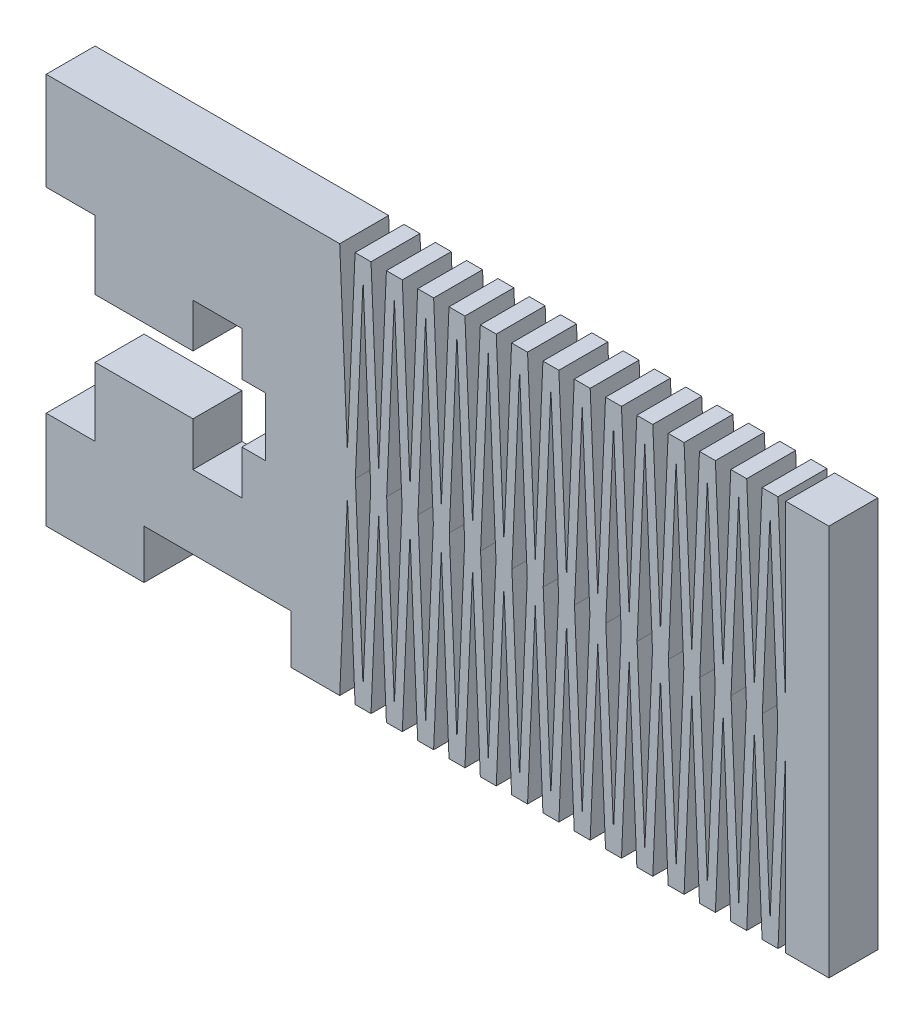
SolidWorks part; units mm, degrees
ref_plane "Front Plane" through (0, 0, 0) normal (0, 0, 1) x (1, 0, 0)
ref_plane "Top Plane" through (0, 0, 0) normal (0, 1, 0) x (1, 0, 0)
ref_plane "Right Plane" through (0, 0, 0) normal (1, 0, 0) x (0, 0, -1)
sketch "Sketch1" plane through (0, 0, 0) normal (0, 0, 1) x (1, 0, 0)
  line L0 (0, 12.7) -> (50.8, 12.7) construction
  line L1 (0, 0) -> (6.35, 0)
  line L2 (0, 0) -> (0, 25.4)
  line L3 (0, 25.4) -> (50.8, 25.4)
  line L4 (50.8, 0) -> (50.8, 25.4)
  line L5 (0, 19.05) -> (3.175, 19.05)
  line L6 (3.175, 19.05) -> (3.175, 14.605)
  line L7 (3.175, 14.605) -> (9.525, 14.605)
  line L8 (9.525, 14.605) -> (9.525, 17.4625)
  line L9 (9.525, 17.4625) -> (12.7, 17.4625)
  line L10 (12.7, 17.4625) -> (12.7, 14.605)
  line L11 (12.7, 14.605) -> (14.224, 14.605)
  line L12 (14.224, 14.605) -> (14.224, 10.795)
  line L13 (12.7, 10.795) -> (14.224, 10.795)
  line L14 (12.7, 7.9375) -> (12.7, 10.795)
  line L15 (9.525, 7.9375) -> (12.7, 7.9375)
  line L16 (19.05, 25.4) -> (19.05, 0) construction
  line L17 (19.05, 13.97) -> (50.8, 13.97) construction
  line L18 (19.05, 11.43) -> (50.8, 11.43) construction
  line L19 (19.05, 25.4) -> (19.549, 13.97)
  line L20 (19.549, 13.97) -> (20.0481, 25.4)
  line L21 (19.549, 13.97) -> (19.549, 25.4) construction
  line L22 (19.05, 24.13) -> (50.8, 24.13) construction
  line L23 (20.565, 24.13) -> (20.066, 12.7)
  line L24 (20.565, 24.13) -> (20.565, 25.4) construction
  line L25 (21.082, 25.4) -> (21.581, 13.97)
  line L26 (20.565, 24.13) -> (21.0641, 12.7)
  line L27 (20.565, 24.13) -> (20.565, 12.7) construction
  line L28 (21.082, 0) -> (21.581, 11.43)
  line L29 (20.565, 1.27) -> (21.0641, 12.7)
  line L30 (20.565, 1.27) -> (20.066, 12.7)
  line L31 (19.549, 11.43) -> (20.0481, 0)
  line L32 (19.05, 0) -> (19.549, 11.43)
  line L33 (21.581, 13.97) -> (22.0801, 25.4)
  line L34 (22.597, 24.13) -> (22.098, 12.7)
  line L35 (22.597, 24.13) -> (23.0961, 12.7)
  line L36 (23.114, 25.4) -> (23.613, 13.97)
  line L37 (21.581, 11.43) -> (22.0801, 0)
  line L38 (22.597, 1.27) -> (22.098, 12.7)
  line L39 (22.597, 1.27) -> (23.0961, 12.7)
  line L40 (23.114, 0) -> (23.613, 11.43)
  line L41 (23.613, 13.97) -> (24.1121, 25.4)
  line L42 (24.629, 24.13) -> (24.13, 12.7)
  line L43 (24.629, 24.13) -> (25.1281, 12.7)
  line L44 (25.146, 25.4) -> (25.645, 13.97)
  line L45 (23.613, 11.43) -> (24.1121, 0)
  line L46 (24.629, 1.27) -> (24.13, 12.7)
  line L47 (24.629, 1.27) -> (25.1281, 12.7)
  line L48 (25.146, 0) -> (25.645, 11.43)
  line L49 (25.645, 13.97) -> (26.1441, 25.4)
  line L50 (26.661, 24.13) -> (26.162, 12.7)
  line L51 (26.661, 24.13) -> (27.1601, 12.7)
  line L52 (27.178, 25.4) -> (27.677, 13.97)
  line L53 (25.645, 11.43) -> (26.1441, 0)
  line L54 (26.661, 1.27) -> (26.162, 12.7)
  line L55 (26.661, 1.27) -> (27.1601, 12.7)
  line L56 (27.178, 0) -> (27.677, 11.43)
  line L57 (27.677, 13.97) -> (28.1761, 25.4)
  line L58 (28.693, 24.13) -> (28.194, 12.7)
  line L59 (28.693, 24.13) -> (29.1921, 12.7)
  line L60 (29.21, 25.4) -> (29.709, 13.97)
  line L61 (27.677, 11.43) -> (28.1761, 0)
  line L62 (28.693, 1.27) -> (28.194, 12.7)
  line L63 (28.693, 1.27) -> (29.1921, 12.7)
  line L64 (29.21, 0) -> (29.709, 11.43)
  line L65 (29.709, 13.97) -> (30.2081, 25.4)
  line L66 (30.725, 24.13) -> (30.226, 12.7)
  line L67 (30.725, 24.13) -> (31.2241, 12.7)
  line L68 (31.242, 25.4) -> (31.741, 13.97)
  line L69 (29.709, 11.43) -> (30.2081, 0)
  line L70 (30.725, 1.27) -> (30.226, 12.7)
  line L71 (30.725, 1.27) -> (31.2241, 12.7)
  line L72 (31.242, 0) -> (31.741, 11.43)
  line L73 (31.741, 13.97) -> (32.2401, 25.4)
  line L74 (32.757, 24.13) -> (32.258, 12.7)
  line L75 (32.757, 24.13) -> (33.2561, 12.7)
  line L76 (33.274, 25.4) -> (33.773, 13.97)
  line L77 (31.741, 11.43) -> (32.2401, 0)
  line L78 (32.757, 1.27) -> (32.258, 12.7)
  line L79 (32.757, 1.27) -> (33.2561, 12.7)
  line L80 (33.274, 0) -> (33.773, 11.43)
  line L81 (33.773, 13.97) -> (34.2721, 25.4)
  line L82 (34.789, 24.13) -> (34.29, 12.7)
  line L83 (34.789, 24.13) -> (35.2881, 12.7)
  line L84 (35.306, 25.4) -> (35.805, 13.97)
  line L85 (33.773, 11.43) -> (34.2721, 0)
  line L86 (34.789, 1.27) -> (34.29, 12.7)
  line L87 (34.789, 1.27) -> (35.2881, 12.7)
  line L88 (35.306, 0) -> (35.805, 11.43)
  line L89 (35.805, 13.97) -> (36.3041, 25.4)
  line L90 (36.821, 24.13) -> (36.322, 12.7)
  line L91 (36.821, 24.13) -> (37.3201, 12.7)
  line L92 (37.338, 25.4) -> (37.837, 13.97)
  line L93 (35.805, 11.43) -> (36.3041, 0)
  line L94 (36.821, 1.27) -> (36.322, 12.7)
  line L95 (36.821, 1.27) -> (37.3201, 12.7)
  line L96 (37.338, 0) -> (37.837, 11.43)
  line L97 (37.837, 13.97) -> (38.3361, 25.4)
  line L98 (38.853, 24.13) -> (38.354, 12.7)
  line L99 (38.853, 24.13) -> (39.3521, 12.7)
  line L100 (39.37, 25.4) -> (39.869, 13.97)
  line L101 (37.837, 11.43) -> (38.3361, 0)
  line L102 (38.853, 1.27) -> (38.354, 12.7)
  line L103 (38.853, 1.27) -> (39.3521, 12.7)
  line L104 (39.37, 0) -> (39.869, 11.43)
  line L105 (39.869, 13.97) -> (40.3681, 25.4)
  line L106 (40.885, 24.13) -> (40.386, 12.7)
  line L107 (40.885, 24.13) -> (41.3841, 12.7)
  line L108 (41.402, 25.4) -> (41.901, 13.97)
  line L109 (39.869, 11.43) -> (40.3681, 0)
  line L110 (40.885, 1.27) -> (40.386, 12.7)
  line L111 (40.885, 1.27) -> (41.3841, 12.7)
  line L112 (41.402, 0) -> (41.901, 11.43)
  line L113 (41.901, 13.97) -> (42.4001, 25.4)
  line L114 (42.917, 24.13) -> (42.418, 12.7)
  line L115 (42.917, 24.13) -> (43.4161, 12.7)
  line L116 (43.434, 25.4) -> (43.933, 13.97)
  line L117 (41.901, 11.43) -> (42.4001, 0)
  line L118 (42.917, 1.27) -> (42.418, 12.7)
  line L119 (42.917, 1.27) -> (43.4161, 12.7)
  line L120 (43.434, 0) -> (43.933, 11.43)
  line L121 (43.933, 13.97) -> (44.4321, 25.4)
  line L122 (44.949, 24.13) -> (44.45, 12.7)
  line L123 (44.949, 24.13) -> (45.4481, 12.7)
  line L124 (45.466, 25.4) -> (45.965, 13.97)
  line L125 (43.933, 11.43) -> (44.4321, 0)
  line L126 (44.949, 1.27) -> (44.45, 12.7)
  line L127 (44.949, 1.27) -> (45.4481, 12.7)
  line L128 (45.466, 0) -> (45.965, 11.43)
  line L129 (45.965, 13.97) -> (46.4641, 25.4)
  line L130 (46.981, 24.13) -> (46.482, 12.7)
  line L131 (46.981, 24.13) -> (47.4801, 12.7)
  line L132 (47.498, 25.4) -> (47.997, 13.97)
  line L133 (45.965, 11.43) -> (46.4641, 0)
  line L134 (46.981, 1.27) -> (46.482, 12.7)
  line L135 (46.981, 1.27) -> (47.4801, 12.7)
  line L136 (47.498, 0) -> (47.997, 11.43)
  line L137 (47.997, 13.97) -> (47.997, 25.4)
  line L138 (47.997, 11.43) -> (47.997, 0)
  line L139 (6.35, 0) -> (6.35, 3.175)
  line L140 (6.35, 3.175) -> (15.875, 3.175)
  line L141 (15.875, 3.175) -> (15.875, 0)
  line L142 (15.875, 0) -> (50.8, 0)
  line L227 (9.525, 10.795) -> (9.525, 7.9375)
  line L228 (3.175, 10.795) -> (9.525, 10.795)
  line L229 (3.175, 6.35) -> (3.175, 10.795)
  line L230 (0, 6.35) -> (3.175, 6.35)
  line L231 (63.237, 24.13) -> (62.738, 12.7) [skipped]
  line L232 (64.253, 13.97) -> (64.7521, 25.4) [skipped]
  line L233 (65.269, 24.13) -> (64.77, 12.7) [skipped]
  line L234 (63.237, 24.13) -> (63.7361, 12.7) [skipped]
  line L235 (67.818, 25.4) -> (68.317, 13.97) [skipped]
  line L236 (69.333, 24.13) -> (68.834, 12.7) [skipped]
  line L237 (69.85, 25.4) -> (70.349, 13.97) [skipped]
  line L238 (69.333, 24.13) -> (69.8321, 12.7) [skipped]
  line L239 (68.317, 13.97) -> (68.8161, 25.4) [skipped]
  line L240 (65.269, 24.13) -> (65.7681, 12.7) [skipped]
  line L241 (63.754, 25.4) -> (64.253, 13.97) [skipped]
  line L242 (68.317, 11.43) -> (68.8161, 0) [skipped]
  line L243 (69.85, 0) -> (70.349, 11.43) [skipped]
  line L244 (67.818, 0) -> (68.317, 11.43) [skipped]
  line L245 (65.269, 1.27) -> (65.7681, 12.7) [skipped]
  line L246 (63.754, 0) -> (64.253, 11.43) [skipped]
  line L247 (61.722, 0) -> (62.221, 11.43) [skipped]
  line L248 (63.237, 1.27) -> (62.738, 12.7) [skipped]
  line L249 (62.221, 11.43) -> (62.7201, 0) [skipped]
  line L250 (65.269, 1.27) -> (64.77, 12.7) [skipped]
  line L251 (65.786, 0) -> (66.285, 11.43) [skipped]
  line L252 (66.285, 11.43) -> (66.7841, 0) [skipped]
  line L253 (67.301, 1.27) -> (66.802, 12.7) [skipped]
  line L254 (67.301, 1.27) -> (67.8001, 12.7) [skipped]
  line L255 (69.333, 1.27) -> (68.834, 12.7) [skipped]
  line L256 (69.333, 1.27) -> (69.8321, 12.7) [skipped]
  line L257 (67.301, 24.13) -> (66.802, 12.7) [skipped]
  line L258 (67.301, 24.13) -> (67.8001, 12.7) [skipped]
  line L259 (66.285, 13.97) -> (66.7841, 25.4) [skipped]
  line L260 (65.786, 25.4) -> (66.285, 13.97) [skipped]
  line L261 (64.253, 11.43) -> (64.7521, 0) [skipped]
  line L262 (63.237, 1.27) -> (63.7361, 12.7) [skipped]
  line L263 (59.173, 1.27) -> (59.6721, 12.7) [skipped]
  line L264 (60.189, 11.43) -> (60.6881, 0) [skipped]
  line L265 (61.205, 1.27) -> (60.706, 12.7) [skipped]
  line L266 (61.205, 1.27) -> (61.7041, 12.7) [skipped]
  line L267 (59.69, 25.4) -> (60.189, 13.97) [skipped]
  line L268 (59.173, 24.13) -> (59.6721, 12.7) [skipped]
  line L269 (61.205, 24.13) -> (61.7041, 12.7) [skipped]
  line L270 (59.173, 24.13) -> (58.674, 12.7) [skipped]
  line L271 (58.157, 13.97) -> (58.6561, 25.4) [skipped]
  line L272 (57.658, 25.4) -> (58.157, 13.97) [skipped]
  line L273 (57.141, 24.13) -> (56.642, 12.7) [skipped]
  line L274 (55.109, 24.13) -> (55.6081, 12.7) [skipped]
  line L275 (54.093, 13.97) -> (54.5921, 25.4) [skipped]
  line L276 (57.141, 1.27) -> (56.642, 12.7) [skipped]
  line L277 (59.69, 0) -> (60.189, 11.43) [skipped]
  line L278 (60.189, 13.97) -> (60.6881, 25.4) [skipped]
  line L279 (61.722, 25.4) -> (62.221, 13.97) [skipped]
  line L280 (56.125, 13.97) -> (56.6241, 25.4) [skipped]
  line L281 (56.125, 11.43) -> (56.6241, 0) [skipped]
  line L282 (57.141, 1.27) -> (57.6401, 12.7) [skipped]
  line L283 (57.141, 24.13) -> (57.6401, 12.7) [skipped]
  line L284 (52.061, 13.97) -> (52.5601, 25.4) [skipped]
  line L285 (53.077, 24.13) -> (52.578, 12.7) [skipped]
  line L286 (51.562, 25.4) -> (52.061, 13.97) [skipped]
  line L287 (51.045, 24.13) -> (51.5441, 12.7) [skipped]
  line L288 (51.045, 1.27) -> (51.5441, 12.7) [skipped]
  line L289 (51.562, 0) -> (52.061, 11.43) [skipped]
  line L290 (52.061, 11.43) -> (52.5601, 0) [skipped]
  line L291 (53.077, 1.27) -> (52.578, 12.7) [skipped]
  line L292 (53.594, 0) -> (54.093, 11.43) [skipped]
  line L293 (53.077, 1.27) -> (53.5761, 12.7) [skipped]
  line L294 (53.077, 24.13) -> (53.5761, 12.7) [skipped]
  line L295 (51.045, 24.13) -> (50.546, 12.7) [skipped]
  line L296 (51.045, 1.27) -> (50.546, 12.7) [skipped]
  line L297 (50.029, 11.43) -> (50.5281, 0) [skipped]
  line L298 (49.53, 25.4) -> (50.029, 13.97) [skipped]
  line L299 (49.53, 0) -> (50.029, 11.43) [skipped]
  line L300 (50.029, 13.97) -> (50.5281, 25.4) [skipped]
  line L301 (49.013, 24.13) -> (49.5121, 12.7) [skipped]
  line L302 (49.013, 1.27) -> (49.5121, 12.7) [skipped]
  line L303 (49.013, 24.13) -> (48.514, 12.7) [skipped]
  line L304 (49.013, 1.27) -> (48.514, 12.7) [skipped]
  line L305 (47.997, 13.97) -> (48.4961, 25.4) [skipped]
  line L306 (47.997, 11.43) -> (48.4961, 0) [skipped]
  line L307 (53.594, 25.4) -> (54.093, 13.97) [skipped]
  line L308 (55.109, 24.13) -> (54.61, 12.7) [skipped]
  line L309 (55.626, 25.4) -> (56.125, 13.97) [skipped]
  line L310 (61.205, 24.13) -> (60.706, 12.7) [skipped]
  line L311 (62.221, 13.97) -> (62.7201, 25.4) [skipped]
  line L312 (54.093, 11.43) -> (54.5921, 0) [skipped]
  line L313 (55.109, 1.27) -> (54.61, 12.7) [skipped]
  line L314 (55.109, 1.27) -> (55.6081, 12.7) [skipped]
  line L315 (55.626, 0) -> (56.125, 11.43) [skipped]
  line L316 (57.658, 0) -> (58.157, 11.43) [skipped]
  line L317 (58.157, 11.43) -> (58.6561, 0) [skipped]
  line L318 (59.173, 1.27) -> (58.674, 12.7) [skipped]
  point P15 (12.7, 12.7)
  point P18 (14.224, 12.7)
  dimension "D1" = 25.4
  dimension "D2" = 50.8
  dimension "D3" = 3.175
  dimension "D4" = 6.35
  dimension "D5" = 3.175
  dimension "D6" = 4.7625
  dimension "D7" = 1.905
  dimension "D8" = 19.05
  dimension "D9" = 1.27
  dimension "D10" = 2.032
  dimension "D11" = 2.5
  dimension "D12" = 2.54
  dimension "D13" = 2.5
  dimension "D14" = 25
  dimension "D15" = 14.224
  dimension "D16" = 12.7
  dimension "D17" = 3.175
  dimension "D18" = 6.35
  dimension "D19" = 9.525
extrude "Boss-Extrude2" add sketch "Sketch1" along normal blind 3.175
equation "\"THICK\"= 1 / 8in"
